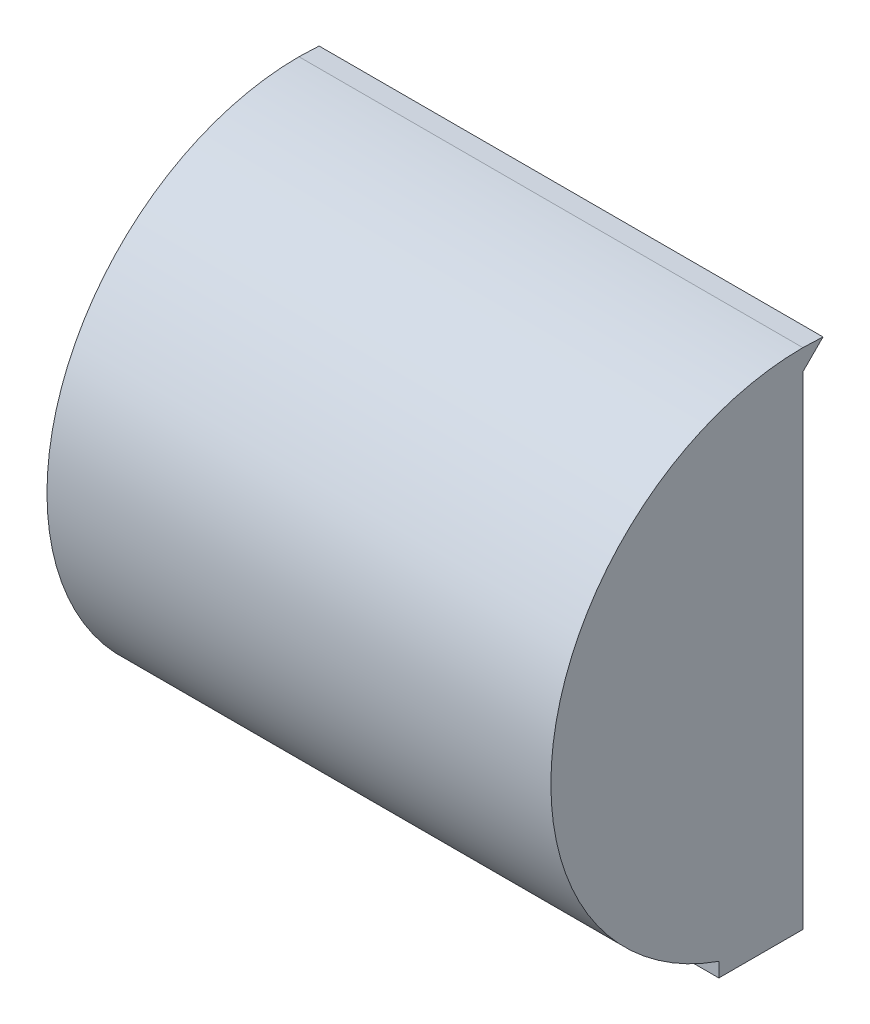
SolidWorks part; units mm, degrees
material "6061-T6 (SS)"
ref_plane "Front Plane" through (0, 0, 0) normal (0, 0, 1) x (1, 0, 0)
ref_plane "Top Plane" through (0, 0, 0) normal (0, 1, 0) x (1, 0, 0)
ref_plane "Right Plane" through (0, 0, 0) normal (1, 0, 0) x (0, 0, -1)
sketch "ExcavatorReferenceSize" plane through (0, 0, 0) normal (0, 1, 0) x (1, 0, 0)
  line L1 (-25.4, -12.7) -> (25.4, -12.7)
  line L2 (-25.4, -12.7) -> (-25.4, 12.7)
  line L3 (-25.4, 12.7) -> (25.4, 12.7)
  line L4 (25.4, -12.7) -> (25.4, 12.7)
  line L5 (-25.4, -12.7) -> (25.4, 12.7) construction
  line L6 (-25.4, 12.7) -> (25.4, -12.7) construction
  point P0 (0, 0)
  dimension "D1" = 25.4
  dimension "D2" = 50.8
sketch "Sketch2" plane through (0, 0, 0) normal (1, 0, 0) x (0, 0, -1)
  line L0 (0, 0) -> (0, 38.1)
  line L1 (0, 0) -> (8.9803, -8.9803) construction
  line L3 (0, 76.2) -> (0, 38.1)
  line L4 (0, 0) -> (0, 87.2631) construction
  arc A2 (0, 76.2) -> (0, 0) centre (0, 38.1) ccw
  dimension "D1" = 76.2
  dimension "D2" = 12.7
  dimension "D3" = 135
extrude "Boss-Extrude1" add sketch "Sketch2" along normal mid plane 76.2
shell "Shell1" thickness 3.175
sketch "Sketch4" plane through (0, 0, 0) normal (1, 0, 0) x (0, 0, -1)
  circle A1 centre (0, -15.875) radius 15.875
  dimension "D1" = 31.75
sketch "Sketch6" plane through (0, 0, 0) normal (1, 0, 0) x (0, 0, -1)
  line L0 (0, 0) -> (0, -15.875) construction
  circle A1 centre (0, -15.875) radius 15.875
ref_plane "Plane2" through (0, 73.025, 0) normal (0, -1, 0) x (-1, 0, 0)
sketch "Sketch7" plane through (0, 0, 0) normal (0, 0, -1) x (1, 0, 0)
  line L0 (38.1, 0) -> (38.1, -76.2) construction
  line L1 (-38.1, 0) -> (38.1, 0)
  line L2 (-38.1, 0) -> (-38.1, -3.175)
  line L3 (-38.1, -3.175) -> (38.1, -3.175)
  line L4 (38.1, 0) -> (38.1, -3.175)
  line L6 (34.925, -3.175) -> (-34.925, -3.175) construction
extrude "Boss-Extrude2" add sketch "Sketch7" against normal blind 12.7
sketch "Sketch8" plane through (38.1, 0, 0) normal (1, 0, 0) x (0, 0, -1)
  line L1 (0, 38.1) -> (3.0525, 76.0775) construction
  line L5 (0, 0) -> (0, 76.2) construction
  line L6 (0, 0) -> (0, 76.2) construction
  line L7 (0, 38.1) -> (0, 73.025) construction
  line L8 (0, 73.025) -> (0, 76.2)
  line L9 (3.0525, 76.0775) -> (0, 73.025)
  line L10 (0, 76.2) -> (3.0525, 76.0775)
  point P2 (6.446, 75.6512)
  point P3 (3.4972, 76.5222)
  point P4 (4.9524, 75.8768)
  dimension "D1" = 38.1
  dimension "D2" = 135
  dimension "D3" = 34.925
extrude "Boss-Extrude3" add sketch "Sketch8" against normal up to surface (76.2 mm away) up to face at (-38.1, 20.9331, 14.1503)
sketch "Sketch10" plane through (0, 0, 0) normal (0, -1, 0) x (1, 0, 0)
  line L0 (0, 0) -> (0, 12.7) construction
  line L1 (0, 6.35) -> (19.05, 6.35) construction
  circle A0 centre (19.05, 6.35) radius 2.0828
  circle A1 centre (-19.05, 6.35) radius 2.0828
  dimension "D3" = 4.1656
  dimension "D1" = 12.7
  dimension "D2" = 19.05
extrude "Cut-Extrude3" cut sketch "Sketch10" against normal up to surface (3.4367 mm away)
sketch "Sketch11" plane through (0, 0, 0) normal (0, -1, 0) x (1, 0, 0)
  circle A0 centre (-19.05, 6.35) radius 2.0828 construction
  circle A1 centre (19.05, 6.35) radius 2.0828 construction
  circle A2 centre (-19.05, 6.35) radius 2.0828 construction
  circle A3 centre (19.05, 6.35) radius 2.0828 construction
  circle A4 centre (19.05, 6.35) radius 3.429
  circle A5 centre (-19.05, 6.35) radius 3.429
  dimension "D1" = 6.858
extrude "Cut-Extrude4" cut sketch "Sketch11" against normal up to surface (0.1224 mm away) from offset 3.175
